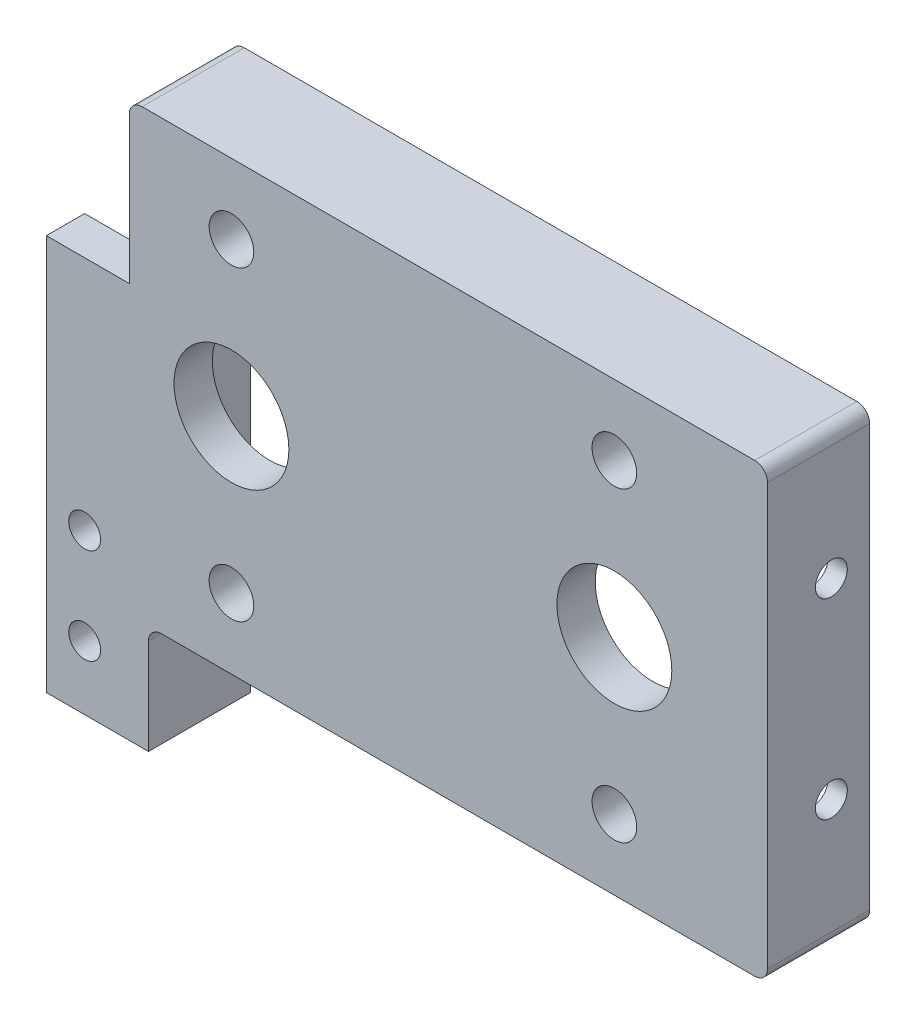
SolidWorks part; units mm, degrees
ref_plane "Front" through (0, 0, 0) normal (0, 0, 1) x (1, 0, 0)
ref_plane "Top" through (0, 0, 0) normal (0, 1, 0) x (1, 0, 0)
ref_plane "Right" through (0, 0, 0) normal (1, 0, 0) x (0, 0, -1)
other "Configuration Table"
sketch "Sketch1" plane through (0, 0, 0) normal (0, 0, 1) x (1, 0, 0)
  line L1 (-54.6575, 16.2329) -> (45.3425, 16.2329)
  line L2 (-54.6575, 16.2329) -> (-54.6575, -47.7671)
  line L3 (-54.6575, -47.7671) -> (45.3425, -47.7671)
  line L4 (45.3425, 16.2329) -> (45.3425, -47.7671)
  dimension "D1" = 100
  dimension "D2" = 64
extrude "Boss-Extrude1" add sketch "Sketch1" along normal blind 6
sketch "Sketch2" plane through (0, 0, 6) normal (0, 0, 1) x (1, 0, 0)
  line L0 (-54.6575, -47.7671) -> (45.3425, -47.7671) construction
  line L1 (-54.6575, 16.2329) -> (-54.6575, -47.7671) construction
  line L2 (-35.6575, 13.1155) -> (-35.6575, -43.0739) construction
  circle A0 centre (-35.6575, -15.7671) radius 9
  circle A1 centre (-35.6575, 8.2329) radius 3.5
  circle A2 centre (-35.6575, -39.7671) radius 3.5
  dimension "D4" = 2
  dimension "D1" = 32
  dimension "D2" = 19
  dimension "D3" = 24
extrude "Cut-Extrude1" cut sketch "Sketch2" against normal blind 10
pattern_linear "LPattern1" count 2 spacing 60 along (1, 0, 0) of "Cut-Extrude1"
sketch "Sketch3" plane through (0, 0, 0) normal (0, 0, -1) x (-1, 0, 0)
  line L0 (54.6575, -47.7671) -> (-45.3425, -47.7671) construction
  line L2 (48.6575, -47.7671) -> (48.6575, 16.2329)
  line L3 (48.6575, 16.2329) -> (51.6575, 16.2329)
  line L4 (51.6575, -47.7671) -> (51.6575, 16.2329)
  line L5 (48.6575, -47.7671) -> (48.6575, -67.7671)
  line L6 (48.6575, -67.7671) -> (51.6575, -67.7671)
  line L7 (51.6575, -67.7671) -> (51.6575, -47.7671)
  line L8 (-45.3425, 16.2329) -> (54.6575, 16.2329) construction
  line L9 (54.6575, 16.2329) -> (54.6575, -47.7671) construction
  dimension "D1" = 3
  dimension "D2" = 20
  dimension "D3" = 3
extrude "Boss-Extrude2" add sketch "Sketch3" along normal blind 10
sketch "Sketch4" plane through (0, -47.7671, 0) normal (0, -1, 0) x (-1, 0, 0)
  line L1 (54.6575, -6) -> (48.6575, -6)
  line L2 (54.6575, -6) -> (54.6575, 0)
  line L3 (54.6575, 0) -> (48.6575, 0)
  line L4 (48.6575, -6) -> (48.6575, 0)
extrude "Boss-Extrude3" add sketch "Sketch4" along normal blind 20
sketch "Sketch5" plane through (0, -47.7671, 0) normal (0, -1, 0) x (-1, 0, 0)
  line L0 (51.6575, 10) -> (51.6575, 0) construction
  line L1 (-45.3425, -6) -> (51.6575, -6)
  line L2 (-45.3425, -6) -> (-45.3425, 10)
  line L3 (-45.3425, 10) -> (51.6575, 10)
  line L4 (51.6575, -6) -> (51.6575, 10)
  line L5 (48.6575, 10) -> (51.6575, 10) construction
extrude "Boss-Extrude4" add sketch "Sketch5" along normal blind 3
pattern_linear "LPattern4" count 2 spacing 67 along (0, 1, 0) of "Boss-Extrude4"
sketch "Sketch6" plane through (45.3425, 0, 0) normal (1, 0, 0) x (0, 0, -1)
  line L1 (-6, 19.2329) -> (10, 19.2329)
  line L2 (-6, 19.2329) -> (-6, -50.7671)
  line L3 (-6, -50.7671) -> (10, -50.7671)
  line L4 (10, 19.2329) -> (10, -50.7671)
extrude "Boss-Extrude5" add sketch "Sketch6" along normal blind 3
sketch "Sketch7" plane through (0, 0, 0) normal (0, 0, -1) x (-1, 0, 0)
  line L1 (51.6575, 16.2329) -> (57.0628, 16.2329)
  line L2 (51.6575, 16.2329) -> (51.6575, -5.7671)
  line L3 (51.6575, -5.7671) -> (57.0628, -5.7671)
  line L4 (57.0628, 16.2329) -> (57.0628, -5.7671)
  dimension "D1" = 22
extrude "Cut-Extrude2" cut sketch "Sketch7" against normal blind 6
sketch "Sketch8" plane through (-54.6575, 0, 0) normal (-1, 0, 0) x (0, 0, 1)
  line L1 (6, -5.7671) -> (0, -5.7671)
  line L2 (6, -5.7671) -> (6, -67.7671)
  line L3 (6, -67.7671) -> (0, -67.7671)
  line L4 (0, -5.7671) -> (0, -67.7671)
extrude "Boss-Extrude6" add sketch "Sketch8" along normal blind 10
sketch "Sketch9" plane through (0, 0, 0) normal (0, 0, -1) x (-1, 0, 0)
  line L0 (64.6575, -67.7671) -> (51.6575, -67.7671) construction
  line L1 (51.6575, -67.7671) -> (51.6575, -5.7671) construction
  circle A0 centre (58.6575, -57.7671) radius 2.5
  dimension "D3" = 5
  dimension "D1" = 10
  dimension "D2" = 7
extrude "Cut-Extrude3" cut sketch "Sketch9" against normal blind 10
pattern_linear "LPattern5" count 2 spacing 15 along (0, 1, 0) of "Cut-Extrude3"
fillet "Fillet1" radius 2 4 edges at (-51.6575, 19.2329, -2) (48.3425, 19.2329, -2) (-48.6575, -50.7671, -2) (48.3425, -50.7671, -2)
sketch "Sketch10" plane through (48.3425, 0, 0) normal (1, 0, 0) x (0, 0, -1)
  line L0 (-6, 19.2329) -> (10, 19.2329) construction
  line L1 (10, -48.7671) -> (10, 17.2329) construction
  circle A0 centre (4, -0.7671) radius 2.5
  point P2 (0, 0)
  dimension "D2" = 5
  dimension "D1" = 20
  dimension "D3" = 6
extrude "Cut-Extrude4" cut sketch "Sketch10" against normal blind 10
pattern_linear "LPattern6" count 2 spacing 30 along (0, -1, 0) of "Cut-Extrude4"
